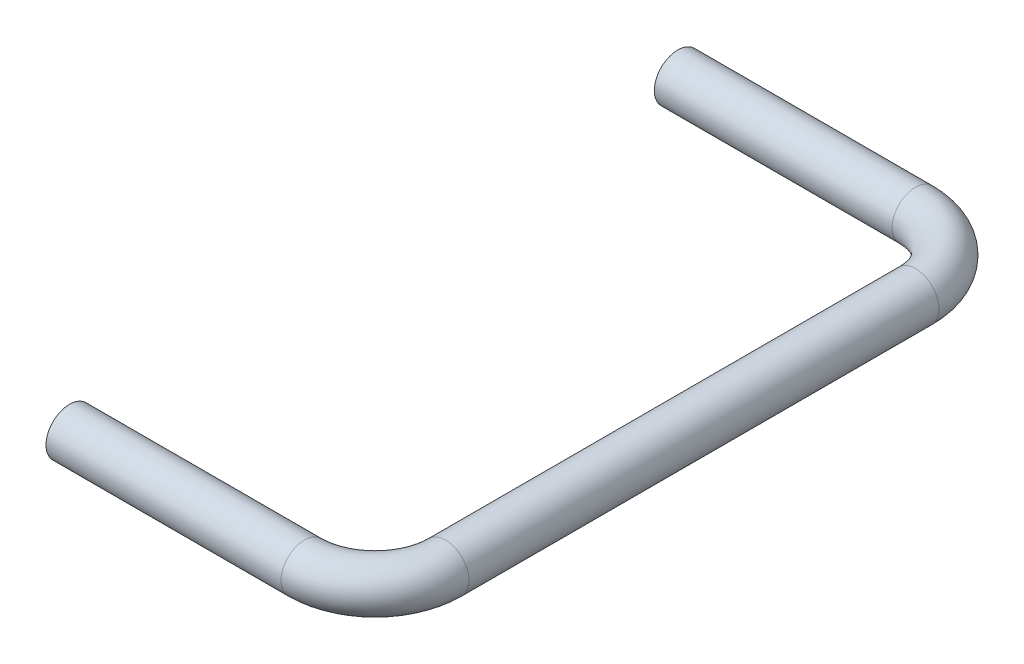
SolidWorks part; units mm, degrees
ref_plane "Спереди" through (0, 0, 0) normal (0, 0, 1) x (1, 0, 0)
ref_plane "Сверху" through (0, 0, 0) normal (0, 1, 0) x (1, 0, 0)
ref_plane "Справа" through (0, 0, 0) normal (1, 0, 0) x (0, 0, -1)
sketch "Эскиз1" plane through (0, 0, 0) normal (1, 0, 0) x (0, 0, -1)
  circle A0 centre (0, 0) radius 1
sketch3d "Трехмерный эскиз1"
  line L0 (0, 0, 0) -> (10, 0, 0)
  line L1 (13, 0, -3) -> (13, 0, -23)
  line L2 (10, 0, -26) -> (-0.1166, 0, -26)
  arc A0 (10, 0, 0) -> (13, 0, -3) centre (10, 0, -3) ccw
  arc A1 (13, 0, -23) -> (10, 0, -26) centre (10, 0, -23) ccw
  point P7 (13, 0, 0)
  point P8 (10, 3, -3)
  point P11 (13, 0, -26)
  point P12 (10, 3, -23)
  dimension "D1" = 3
sweep "По траектории1" add profiles "Эскиз1" path "Трехмерный эскиз1"
